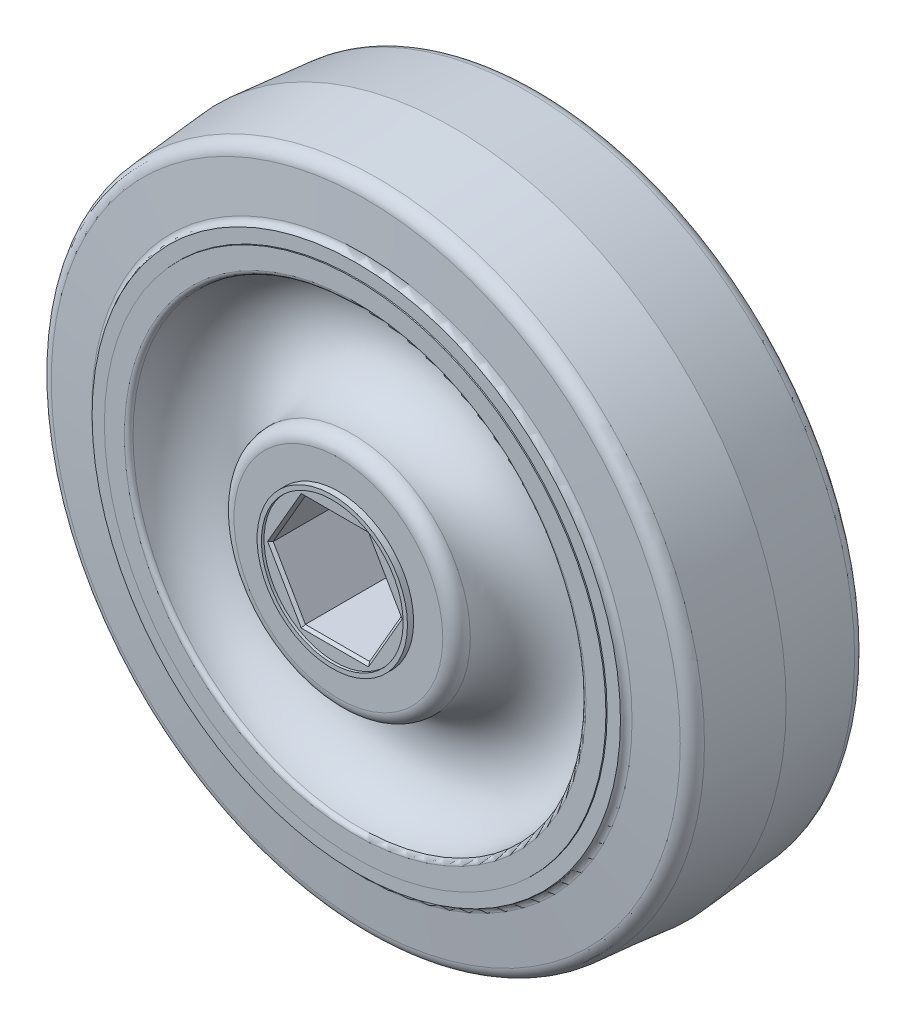
SolidWorks part; units mm, degrees
ref_plane "Front Plane" through (0, 0, 0) normal (0, 0, 1) x (1, 0, 0)
ref_plane "Top Plane" through (0, 0, 0) normal (0, 1, 0) x (1, 0, 0)
ref_plane "Right Plane" through (0, 0, 0) normal (1, 0, 0) x (0, 0, -1)
sketch "Sketch1" plane through (0, 0, 0) normal (0, 1, 0) x (1, 0, 0)
  line L0 (13.79, 13.0937) -> (0, 13.0937)
  line L1 (0, 13.0937) -> (0, -13.0937)
  line L2 (0, -13.0937) -> (13.79, -13.0937)
  line L3 (25.8892, -11.176) -> (28.6737, -11.176)
  line L4 (28.6737, -11.176) -> (28.9266, -6.35)
  line L5 (28.9266, -6.35) -> (28.9306, -6.35)
  line L6 (28.9306, -6.35) -> (28.6843, -11.049)
  line L7 (28.6843, -11.049) -> (30.2083, -11.049)
  line L8 (30.8945, -10.4094) -> (37.2378, -9.8544)
  line L9 (37.2378, -9.8544) -> (38.1, 0)
  line L10 (38.1, 0) -> (37.2378, 9.8544)
  line L11 (37.2378, 9.8544) -> (30.8945, 10.4094)
  line L12 (30.2083, 11.049) -> (28.6843, 11.049)
  line L13 (28.6843, 11.049) -> (28.9306, 6.35)
  line L14 (28.9306, 6.35) -> (28.9266, 6.35)
  line L15 (28.9266, 6.35) -> (28.6737, 11.176)
  line L16 (28.6737, 11.176) -> (25.8892, 11.176)
  line L17 (0, 13.0937) -> (0, -13.0937) construction
  arc A0 (13.79, -13.0937) -> (25.8892, -11.176) centre (19.6675, -11.049) cw
  arc A1 (30.2083, -11.049) -> (30.8945, -10.4094) centre (30.9609, -11.1685) cw
  arc A2 (30.8945, 10.4094) -> (30.2083, 11.049) centre (30.9609, 11.1685) cw
  arc A3 (25.8892, 11.176) -> (13.79, 13.0937) centre (19.6675, 11.049) cw
revolve "Revolve1" add sketch "Sketch1" angle 360 about L17
sketch "Sketch2" plane through (0, 0, 13.0937) normal (0, 0, 1) x (1, 0, 0)
  circle A0 centre (0, 0) radius 8.6035
extrude "Boss-Extrude1" add sketch "Sketch2" along normal blind 0.7001 draft 0.5
sketch "Sketch3" plane through (0, 0, -13.0937) normal (0, 0, -1) x (-1, 0, 0)
  circle A0 centre (0, 0) radius 8.6035
extrude "Boss-Extrude2" add sketch "Sketch3" along normal blind 0.7001 draft 0.5
hole_wizard "Hole1" positions "Sketch5" profile "Sketch4" legacy
sketch "Sketch5" plane through (0, 0, 13.7937) normal (0, 0, 1) x (1, 0, 0)
  point P0 (0, 0)
sketch "Sketch4" plane through (0, 0, 13.7937) normal (1, 0, 0) x (0, -1, 0)
  line L0 (0, 0) -> (0, 0.3)
  line L1 (0, 0.3) -> (8.1, 0.3)
  line L2 (8.1, 0.3) -> (8.1026, 0)
  line L3 (8.1026, 0) -> (0, 0)
  line L4 (0, 110) -> (0, -10) construction
  dimension "Minor Diameter" = 16.2
  dimension "Depth" = 0.3
  dimension "Major Diameter" = 16.2052
hole_wizard "Hole2" positions "Sketch7" profile "Sketch6" legacy
sketch "Sketch7" plane through (0, 0, -13.7937) normal (0, 0, -1) x (-1, 0, 0)
  point P0 (0, 0)
sketch "Sketch6" plane through (0, 0, -13.7937) normal (1, 0, 0) x (0, 1, 0)
  line L0 (0, 0) -> (0, 0.3)
  line L1 (0, 0.3) -> (8.1, 0.3)
  line L2 (8.1, 0.3) -> (8.1026, 0)
  line L3 (8.1026, 0) -> (0, 0)
  line L4 (0, 110) -> (0, -10) construction
  dimension "Minor Diameter" = 16.2
  dimension "Depth" = 0.3
  dimension "Major Diameter" = 16.2052
sketch "Sketch8" plane through (0, 0, -13.4937) normal (0, 0, -1) x (-1, 0, 0)
  line L0 (-7.347, 0) -> (-3.6735, -6.3627)
  line L1 (-3.6735, -6.3627) -> (3.6735, -6.3627)
  line L2 (3.6735, -6.3627) -> (7.347, 0)
  line L3 (7.347, 0) -> (3.6735, 6.3627)
  line L4 (3.6735, 6.3627) -> (-3.6735, 6.3627)
  line L5 (-3.6735, 6.3627) -> (-7.347, 0)
extrude "Cut-Extrude1" cut sketch "Sketch8" against normal through all
chamfer "Chamfer1" distance 0.3 angle 45 12 edges at (-5.5103, -3.1814, -13.4937) (0, -6.3627, -13.4937) (-5.5103, 3.1813, -13.4937) (5.5103, -3.1813, -13.4937) (0, 6.3627, -13.4937) (5.5103, 3.1814, -13.4937) (5.5103, -3.1813, 13.4937) (5.5103, 3.1814, 13.4937) (0, -6.3627, 13.4937) (0, 6.3627, 13.4937) (-5.5103, -3.1814, 13.4937) (-5.5103, 3.1813, 13.4937)
fillet "Fillet1" radius 0.508 2 edges at (25.8892, 0, 11.176) (25.8892, 0, -11.176)
fillet "Fillet2" radius 1.524 4 edges at (13.79, 0, 13.0937) (37.2378, 0, -9.8544) (37.2378, 0, 9.8544) (13.79, 0, -13.0937)
